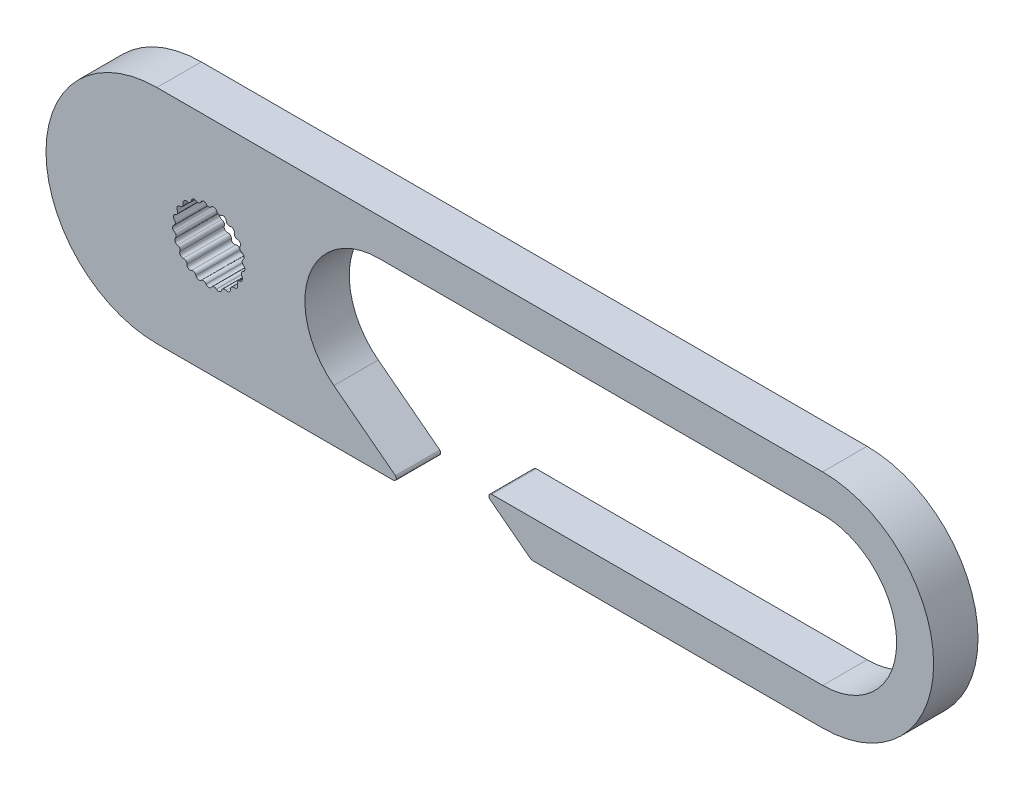
SolidWorks part; units mm, degrees
ref_plane "Front Plane" through (0, 0, 0) normal (0, 0, 1) x (1, 0, 0)
ref_plane "Top Plane" through (0, 0, 0) normal (0, 1, 0) x (1, 0, 0)
ref_plane "Right Plane" through (0, 0, 0) normal (1, 0, 0) x (0, 0, -1)
sketch "Sketch2" plane through (0, 0, 0) normal (0, 0, 1) x (1, 0, 0)
  line L0 (5.2704, 0.8557) -> (54.3236, 0.8557) construction
  line L1 (16.7704, 5.8557) -> (46.7704, 5.8557)
  line L2 (24.4073, -4.1443) -> (46.7704, -4.1443)
  line L3 (1.7704, 8.3557) -> (46.7704, 8.3557)
  line L4 (1.7704, -6.6443) -> (17.7478, -6.6443)
  line L5 (1.7704, 5.8557) -> (46.7704, 5.8557) construction
  line L6 (1.7704, -4.1443) -> (46.7704, -4.1443) construction
  line L7 (11.7704, 0.8557) -> (46.7704, 0.8557) construction
  line L8 (13.728, -3.1122) -> (17.8892, -6.3029)
  line L10 (26.9436, -6.5411) -> (24.2856, -4.5031)
  line L12 (27.2478, -6.6443) -> (46.7704, -6.6443)
  line L13 (1.7704, -6.6443) -> (46.7704, -6.6443) construction
  arc A1 (46.7704, -4.1443) -> (46.7704, 5.8557) centre (46.7704, 0.8557) ccw
  arc A2 (46.7704, -6.6443) -> (46.7704, 8.3557) centre (46.7704, 0.8557) ccw
  arc A3 (1.7704, 8.3557) -> (1.7704, -6.6443) centre (1.7704, 0.8557) ccw
  circle A4 centre (5.2704, 0.8557) radius 2.5
  arc A6 (16.7704, 5.8557) -> (13.728, -3.1122) centre (16.7704, 0.8557) ccw
  arc A7 (1.7704, 5.8557) -> (1.7704, -4.1443) centre (1.7704, 0.8557) ccw construction
  arc A8 (24.2856, -4.5031) -> (24.4073, -4.1443) centre (24.4073, -4.3443) cw
  arc A9 (27.2478, -6.6443) -> (26.9436, -6.5411) centre (27.2478, -6.1443) cw
  arc A10 (17.7478, -6.6443) -> (17.8892, -6.3029) centre (17.7478, -6.4443) ccw
  circle A11 centre (5.2704, 0.8557) radius 2.2653 construction
  arc A12 (5.1037, 3.2008) -> (5.2704, 3.1209) centre (5.2704, 3.3347) ccw
  arc A13 (5.1037, 3.2008) -> (4.7384, 3.1457) centre (4.9371, 3.0669) ccw
  arc A14 (4.6027, 3.0203) -> (4.7384, 3.1457) centre (4.5397, 3.2245) ccw
  arc A15 (5.2704, 3.1209) -> (5.437, 3.2008) centre (5.2704, 3.3347) ccw
  arc A16 (5.8024, 3.1457) -> (5.437, 3.2008) centre (5.6037, 3.0669) ccw
  arc A17 (5.8024, 3.1457) -> (5.9381, 3.0203) centre (6.0011, 3.2245) ccw
  arc A18 (5.9381, 3.0203) -> (6.1209, 3.0475) centre (6.0011, 3.2245) ccw
  arc A19 (6.4537, 2.8872) -> (6.1209, 3.0475) centre (6.2406, 2.8704) ccw
  arc A20 (6.4537, 2.8872) -> (6.5464, 2.7273) centre (6.6669, 2.9039) ccw
  arc A21 (6.5464, 2.7273) -> (6.7291, 2.6994) centre (6.6669, 2.9039) ccw
  arc A22 (7, 2.4481) -> (6.7291, 2.6994) centre (6.7914, 2.4949) ccw
  arc A23 (7, 2.4481) -> (7.0414, 2.268) centre (7.2086, 2.4013) ccw
  arc A24 (7.0414, 2.268) -> (7.2078, 2.1875) centre (7.2086, 2.4013) ccw
  arc A25 (7.3925, 1.8676) -> (7.2078, 2.1875) centre (7.207, 1.9738) ccw
  arc A26 (7.3925, 1.8676) -> (7.379, 1.6832) centre (7.578, 1.7613) ccw
  arc A27 (7.379, 1.6832) -> (7.5143, 1.5573) centre (7.578, 1.7613) ccw
  arc A28 (7.5965, 1.1971) -> (7.5143, 1.5573) centre (7.4505, 1.3533) ccw
  arc A29 (7.5965, 1.1971) -> (7.5293, 1.0249) centre (7.7425, 1.0409) ccw
  arc A30 (7.5293, 1.0249) -> (7.6214, 0.8647) centre (7.7425, 1.0409) ccw
  arc A31 (7.5938, 0.4963) -> (7.6214, 0.8647) centre (7.5004, 0.6885) ccw
  arc A32 (7.5938, 0.4963) -> (7.4788, 0.3516) centre (7.6872, 0.304) ccw
  arc A33 (7.4788, 0.3516) -> (7.5196, 0.1713) centre (7.6872, 0.304) ccw
  arc A34 (7.3846, -0.1726) -> (7.5196, 0.1713) centre (7.352, 0.0387) ccw
  arc A35 (7.3846, -0.1726) -> (7.2321, -0.277) centre (7.4173, -0.3839) ccw
  arc A36 (7.2321, -0.277) -> (7.218, -0.4612) centre (7.4173, -0.3839) ccw
  arc A37 (6.9876, -0.7501) -> (7.218, -0.4612) centre (7.0187, -0.5386) ccw
  arc A38 (6.9876, -0.7501) -> (6.8111, -0.8049) centre (6.9565, -0.9616) ccw
  arc A39 (6.8111, -0.8049) -> (6.7433, -0.9768) centre (6.9565, -0.9616) ccw
  arc A40 (6.438, -1.1849) -> (6.7433, -0.9768) centre (6.5301, -0.992) ccw
  arc A41 (6.438, -1.1849) -> (6.2532, -1.1853) centre (6.346, -1.3779) ccw
  arc A42 (6.2532, -1.1853) -> (6.1377, -1.3295) centre (6.346, -1.3779) ccw
  arc A43 (5.7847, -1.4385) -> (6.1377, -1.3295) centre (5.9295, -1.2812) ccw
  arc A44 (5.7847, -1.4385) -> (5.608, -1.3843) centre (5.6398, -1.5957) ccw
  arc A45 (5.608, -1.3843) -> (5.4551, -1.4881) centre (5.6398, -1.5957) ccw
  arc A46 (5.0856, -1.4881) -> (5.4551, -1.4881) centre (5.2704, -1.3806) ccw
  arc A47 (5.0856, -1.4881) -> (4.9328, -1.3843) centre (4.9009, -1.5957) ccw
  arc A48 (4.9328, -1.3843) -> (4.7561, -1.4385) centre (4.9009, -1.5957) ccw
  arc A49 (4.403, -1.3295) -> (4.7561, -1.4385) centre (4.6112, -1.2812) ccw
  arc A50 (4.403, -1.3295) -> (4.2875, -1.1853) centre (4.1948, -1.3779) ccw
  arc A51 (4.2875, -1.1853) -> (4.1027, -1.1849) centre (4.1948, -1.3779) ccw
  arc A52 (3.7974, -0.9768) -> (4.1027, -1.1849) centre (4.0107, -0.992) ccw
  arc A53 (3.7974, -0.9768) -> (3.7296, -0.8049) centre (3.5842, -0.9616) ccw
  arc A54 (3.7296, -0.8049) -> (3.5531, -0.7501) centre (3.5842, -0.9616) ccw
  arc A55 (3.3227, -0.4612) -> (3.5531, -0.7501) centre (3.522, -0.5386) ccw
  arc A56 (3.3227, -0.4612) -> (3.3086, -0.277) centre (3.1235, -0.3839) ccw
  arc A57 (3.3086, -0.277) -> (3.1561, -0.1726) centre (3.1235, -0.3839) ccw
  arc A58 (3.0211, 0.1713) -> (3.1561, -0.1726) centre (3.1887, 0.0387) ccw
  arc A59 (3.0211, 0.1713) -> (3.0619, 0.3516) centre (2.8535, 0.304) ccw
  arc A60 (3.0619, 0.3516) -> (2.9469, 0.4963) centre (2.8535, 0.304) ccw
  arc A61 (2.9193, 0.8647) -> (2.9469, 0.4963) centre (3.0404, 0.6885) ccw
  arc A62 (2.9193, 0.8647) -> (3.0114, 1.0249) centre (2.7983, 1.0409) ccw
  arc A63 (3.0114, 1.0249) -> (2.9442, 1.1971) centre (2.7983, 1.0409) ccw
  arc A64 (3.0265, 1.5573) -> (2.9442, 1.1971) centre (3.0902, 1.3533) ccw
  arc A65 (3.0265, 1.5573) -> (3.1617, 1.6832) centre (2.9627, 1.7613) ccw
  arc A66 (3.1617, 1.6832) -> (3.1482, 1.8676) centre (2.9627, 1.7613) ccw
  arc A67 (3.333, 2.1875) -> (3.1482, 1.8676) centre (3.3337, 1.9738) ccw
  arc A68 (3.333, 2.1875) -> (3.4993, 2.268) centre (3.3322, 2.4013) ccw
  arc A69 (3.4993, 2.268) -> (3.5408, 2.4481) centre (3.3322, 2.4013) ccw
  arc A70 (3.8116, 2.6994) -> (3.5408, 2.4481) centre (3.7493, 2.4949) ccw
  arc A71 (3.8116, 2.6994) -> (3.9943, 2.7273) centre (3.8739, 2.9039) ccw
  arc A72 (3.9943, 2.7273) -> (4.087, 2.8872) centre (3.8739, 2.9039) ccw
  arc A73 (4.4199, 3.0475) -> (4.087, 2.8872) centre (4.3001, 2.8704) ccw
  arc A74 (4.4199, 3.0475) -> (4.6027, 3.0203) centre (4.5397, 3.2245) ccw
  point P3 (25, 0)
  point P32 (5.2704, 0.8557)
  point P34 (5.2704, 0.8557)
  point P159 (5.2704, 0.8557)
  point P160 (0, 0)
  point P161 (0, 0)
  dimension "D2" = 30
  dimension "D3" = 45
  dimension "D5" = 5
  dimension "D6" = 5
  dimension "D7" = 5
  dimension "D8" = 0.2
  dimension "D9" = 0.5
  dimension "D10" = 0.2
  dimension "D1" = 2.5
  dimension "D4" = 3.5
  dimension "D11" = 9.5
  dimension "D12" = 2.2362
extrude "Boss-Extrude1" add sketch "Sketch2" along normal blind 3
